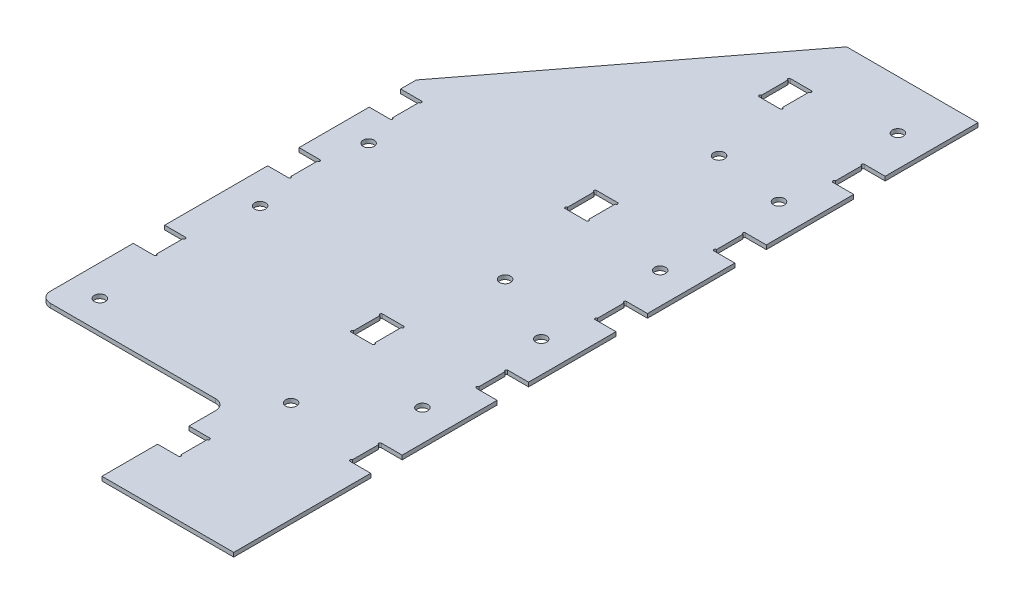
SolidWorks part; units mm, degrees
material "Ti-6Al-4VSolution treated and aged (SS)"
ref_plane "Front Plane" through (0, 0, 0) normal (0, 0, 1) x (1, 0, 0)
ref_plane "Top Plane" through (0, 0, 0) normal (0, 1, 0) x (1, 0, 0)
ref_plane "Right Plane" through (0, 0, 0) normal (1, 0, 0) x (0, 0, -1)
sketch "Sketch1" plane through (0, 0, 0) normal (0, 1, 0) x (1, 0, 0)
  line L0 (0, 0) -> (-80.9625, 0)
  line L1 (-80.9625, 0) -> (-80.9625, 76.2)
  line L3 (-80.9625, 76.2) -> (-195.2625, 76.2)
  line L5 (-195.2625, 76.2) -> (-195.2625, 307.3581)
  line L6 (-195.2625, 307.3581) -> (-80.645, 457.2)
  line L7 (-80.645, 457.2) -> (0, 457.2)
  line L8 (0, 457.2) -> (0, 0)
  dimension "D1" = 76.2
  dimension "D2" = 114.3
  dimension "D3" = 80.9625
  dimension "D4" = 457.2
  dimension "D5" = 231.1581
  dimension "D6" = 80.645
extrude "Boss-Extrude1" add sketch "Sketch1" along normal blind 2.54
fillet "Fillet1" radius 6.35 2 edges at (-195.2625, 1.27, -76.2) (-80.9625, 1.27, -76.2)
sketch "Sketch2" plane through (0, 2.54, 0) normal (0, 1, 0) x (1, 0, 0)
  line L0 (-80.9625, 69.85) -> (-80.9625, 0) construction
  line L1 (-68.2625, 34.29) -> (-80.9625, 34.29)
  line L2 (-68.2625, 34.29) -> (-68.2625, 53.34)
  line L3 (-68.2625, 53.34) -> (-80.9625, 53.34)
  line L4 (-80.9625, 34.29) -> (-80.9625, 53.34)
  line L5 (-80.9625, 53.34) -> (-68.2625, 53.34) construction
  line L6 (0, 0) -> (0, 457.2) construction
  line L7 (-12.7, 84.2962) -> (0, 84.2962)
  line L8 (-12.7, 84.2962) -> (-12.7, 103.3462)
  line L9 (-12.7, 103.3462) -> (0, 103.3462)
  line L10 (0, 84.2962) -> (0, 103.3462)
  line L11 (-12.7, 103.3462) -> (0, 103.3462) construction
  line L12 (-195.2625, 152.7175) -> (-182.5625, 152.7175) construction
  line L13 (-68.2625, 153.3525) -> (-80.9625, 153.3525)
  line L14 (-68.2625, 153.3525) -> (-68.2625, 172.4025)
  line L15 (-68.2625, 172.4025) -> (-80.9625, 172.4025)
  line L16 (-80.9625, 153.3525) -> (-80.9625, 172.4025)
  line L17 (-182.5625, 133.6675) -> (-195.2625, 133.6675)
  line L18 (-182.5625, 133.6675) -> (-182.5625, 152.7175)
  line L19 (-182.5625, 152.7175) -> (-195.2625, 152.7175)
  line L20 (-195.2625, 133.6675) -> (-195.2625, 152.7175)
  line L21 (-195.2625, 307.3581) -> (-195.2625, 82.55) construction
  line L22 (-195.2625, 235.2675) -> (-182.5625, 235.2675) construction
  line L23 (-182.5625, 216.2175) -> (-195.2625, 216.2175)
  line L24 (-182.5625, 216.2175) -> (-182.5625, 235.2675)
  line L25 (-182.5625, 235.2675) -> (-195.2625, 235.2675)
  line L26 (-195.2625, 216.2175) -> (-195.2625, 235.2675)
  line L27 (-195.2625, 297.6648) -> (-182.5625, 297.6648) construction
  line L28 (-182.5625, 278.6148) -> (-195.2625, 278.6148)
  line L29 (-182.5625, 278.6148) -> (-182.5625, 297.6648)
  line L30 (-182.5625, 297.6648) -> (-195.2625, 297.6648)
  line L31 (-195.2625, 278.6148) -> (-195.2625, 297.6648)
  line L32 (-12.7, 180.975) -> (0, 180.975) construction
  line L33 (-68.2625, 284.7975) -> (-80.9625, 284.7975)
  line L34 (-68.2625, 284.7975) -> (-68.2625, 303.8475)
  line L35 (-68.2625, 303.8475) -> (-80.9625, 303.8475)
  line L36 (-80.9625, 284.7975) -> (-80.9625, 303.8475)
  line L37 (-12.7, 161.925) -> (0, 161.925)
  line L38 (-12.7, 161.925) -> (-12.7, 180.975)
  line L39 (-12.7, 180.975) -> (0, 180.975)
  line L40 (0, 161.925) -> (0, 180.975)
  line L41 (-12.7, 254) -> (0, 254) construction
  line L42 (-12.7, 234.95) -> (0, 234.95)
  line L43 (-12.7, 234.95) -> (-12.7, 254)
  line L44 (-12.7, 254) -> (0, 254)
  line L45 (0, 234.95) -> (0, 254)
  line L46 (-12.7, 327.025) -> (0, 327.025) construction
  line L47 (-12.7, 307.975) -> (0, 307.975)
  line L48 (-12.7, 307.975) -> (-12.7, 327.025)
  line L49 (-12.7, 327.025) -> (0, 327.025)
  line L50 (0, 307.975) -> (0, 327.025)
  line L51 (-12.7, 400.05) -> (0, 400.05) construction
  line L52 (-12.7, 381) -> (0, 381)
  line L53 (-12.7, 381) -> (-12.7, 400.05)
  line L54 (-12.7, 400.05) -> (0, 400.05)
  line L55 (0, 381) -> (0, 400.05)
  line L56 (-81.0895, 403.733) -> (-81.0895, 423.037)
  line L57 (-80.9625, 403.86) -> (-68.2625, 403.86)
  line L58 (-80.9625, 403.86) -> (-80.9625, 422.91)
  line L59 (-80.9625, 422.91) -> (-68.2625, 422.91)
  line L60 (-68.2625, 403.86) -> (-68.2625, 422.91)
  line L61 (-81.0895, 423.037) -> (-68.1355, 423.037)
  line L62 (-68.1355, 403.733) -> (-68.1355, 423.037)
  line L63 (-81.0895, 403.733) -> (-68.1355, 403.733)
  line L64 (-182.4355, 297.7918) -> (-195.3895, 297.7918)
  line L65 (-195.3895, 278.4878) -> (-195.3895, 297.7918)
  line L66 (-182.4355, 278.4878) -> (-195.3895, 278.4878)
  line L67 (-182.4355, 278.4878) -> (-182.4355, 297.7918)
  line L68 (-68.1355, 303.9745) -> (-81.0895, 303.9745)
  line L69 (-81.0895, 284.6705) -> (-81.0895, 303.9745)
  line L70 (-68.1355, 284.6705) -> (-81.0895, 284.6705)
  line L71 (-68.1355, 284.6705) -> (-68.1355, 303.9745)
  line L72 (-182.4355, 235.3945) -> (-195.3895, 235.3945)
  line L73 (-195.3895, 216.0905) -> (-195.3895, 235.3945)
  line L74 (-182.4355, 216.0905) -> (-195.3895, 216.0905)
  line L75 (-182.4355, 216.0905) -> (-182.4355, 235.3945)
  line L76 (-182.4355, 152.8445) -> (-195.3895, 152.8445)
  line L77 (-195.3895, 133.5405) -> (-195.3895, 152.8445)
  line L78 (-182.4355, 133.5405) -> (-195.3895, 133.5405)
  line L79 (-182.4355, 133.5405) -> (-182.4355, 152.8445)
  line L80 (-68.1355, 172.5295) -> (-81.0895, 172.5295)
  line L81 (-81.0895, 153.2255) -> (-81.0895, 172.5295)
  line L82 (-68.1355, 153.2255) -> (-81.0895, 153.2255)
  line L83 (-68.1355, 153.2255) -> (-68.1355, 172.5295)
  line L84 (-68.1355, 53.467) -> (-81.0895, 53.467)
  line L85 (-81.0895, 34.163) -> (-81.0895, 53.467)
  line L86 (-68.1355, 34.163) -> (-81.0895, 34.163)
  line L87 (-68.1355, 34.163) -> (-68.1355, 53.467)
  line L88 (-12.827, 103.4732) -> (0.127, 103.4732)
  line L89 (0.127, 84.1692) -> (0.127, 103.4732)
  line L90 (-12.827, 84.1692) -> (0.127, 84.1692)
  line L91 (-12.827, 84.1692) -> (-12.827, 103.4732)
  line L92 (-12.827, 181.102) -> (0.127, 181.102)
  line L93 (0.127, 161.798) -> (0.127, 181.102)
  line L94 (-12.827, 161.798) -> (0.127, 161.798)
  line L95 (-12.827, 161.798) -> (-12.827, 181.102)
  line L96 (-12.827, 254.127) -> (0.127, 254.127)
  line L97 (0.127, 234.823) -> (0.127, 254.127)
  line L98 (-12.827, 234.823) -> (0.127, 234.823)
  line L99 (-12.827, 234.823) -> (-12.827, 254.127)
  line L100 (-12.827, 327.152) -> (0.127, 327.152)
  line L101 (0.127, 307.848) -> (0.127, 327.152)
  line L102 (-12.827, 307.848) -> (0.127, 307.848)
  line L103 (-12.827, 307.848) -> (-12.827, 327.152)
  line L104 (-12.827, 400.177) -> (0.127, 400.177)
  line L105 (0.127, 380.873) -> (0.127, 400.177)
  line L106 (-12.827, 380.873) -> (0.127, 380.873)
  line L107 (-12.827, 380.873) -> (-12.827, 400.177)
  dimension "D1" = 0.127
extrude "Cut-Extrude1" cut sketch "Sketch2" against normal through all
hole_wizard "1/4 Clearance Hole1" positions "Sketch4" profile "Sketch3" hole size "1/4" standard "ANSI Inch" end condition through all
sketch "Sketch4" plane through (0, 0, 0) normal (0, -1, 0) x (-1, 0, 0)
  point P0 (61.9125, 97.155)
  point P3 (19.05, 134.9375)
  point P6 (19.05, 207.9625)
  point P9 (61.9125, 228.6)
  point P12 (19.05, 280.9875)
  point P15 (19.05, 354.0125)
  point P18 (61.9125, 360.045)
  point P21 (19.05, 427.0375)
  point P24 (176.2125, 259.08)
  point P27 (176.2125, 192.405)
  point P30 (176.2125, 93.98)
sketch "Sketch3" plane through (-61.9125, 0, -97.155) normal (1, 0, 0) x (0, 0, -1)
  line L0 (0, 0) -> (0, 2.54)
  line L1 (0, 2.54) -> (3.3782, 2.54)
  line L2 (3.3782, 2.54) -> (3.3782, 0)
  line L5 (3.3782, 0) -> (0, 0)
  line L11 (0, -6.35) -> (0, 107.95) construction
  dimension "Thru Hole Dia." = 6.7564
  dimension "Thru Hole Depth" = 2.54
sketch "Sketch5" plane through (0, 2.54, 0) normal (0, 1, 0) x (1, 0, 0)
  line L0 (-182.4355, 278.4878) -> (-182.4355, 297.7918) construction
  line L1 (-182.4355, 216.0905) -> (-182.4355, 235.3945) construction
  line L2 (-182.4355, 133.5405) -> (-182.4355, 152.8445) construction
  line L3 (-68.1355, 34.163) -> (-68.1355, 53.467) construction
  line L4 (-12.827, 103.4732) -> (-12.827, 84.1692) construction
  line L5 (-68.1355, 153.2255) -> (-68.1355, 172.5295) construction
  line L6 (-81.0895, 172.5295) -> (-81.0895, 153.2255) construction
  line L7 (-12.827, 181.102) -> (-12.827, 161.798) construction
  line L8 (-12.827, 254.127) -> (-12.827, 234.823) construction
  line L9 (-68.1355, 284.6705) -> (-68.1355, 303.9745) construction
  line L10 (-81.0895, 303.9745) -> (-81.0895, 284.6705) construction
  line L11 (-12.827, 327.152) -> (-12.827, 307.848) construction
  line L12 (-12.827, 400.177) -> (-12.827, 380.873) construction
  line L13 (-68.1355, 403.733) -> (-68.1355, 423.037) construction
  line L14 (-81.0895, 423.037) -> (-81.0895, 403.733) construction
  circle A0 centre (-182.4355, 296.9981) radius 0.7938
  circle A1 centre (-182.4355, 279.2816) radius 0.7938
  circle A2 centre (-182.4355, 234.6007) radius 0.7938
  circle A3 centre (-182.4355, 216.8842) radius 0.7938
  circle A4 centre (-182.4355, 152.0507) radius 0.7938
  circle A5 centre (-182.4355, 134.3342) radius 0.7938
  circle A6 centre (-68.1355, 52.6732) radius 0.7937
  circle A7 centre (-68.1355, 34.9567) radius 0.7937
  circle A8 centre (-12.827, 84.963) radius 0.7937
  circle A9 centre (-12.827, 102.6795) radius 0.7937
  circle A10 centre (-68.1355, 171.7357) radius 0.7937
  circle A11 centre (-81.0895, 171.7357) radius 0.7937
  circle A12 centre (-81.0895, 154.0192) radius 0.7937
  circle A13 centre (-68.1355, 154.0192) radius 0.7937
  circle A14 centre (-12.827, 162.5917) radius 0.7937
  circle A15 centre (-12.827, 180.3082) radius 0.7937
  circle A16 centre (-12.827, 235.6167) radius 0.7937
  circle A17 centre (-12.827, 253.3332) radius 0.7938
  circle A18 centre (-68.1355, 285.4642) radius 0.7937
  circle A19 centre (-81.0895, 285.4642) radius 0.7937
  circle A20 centre (-81.0895, 303.1807) radius 0.7937
  circle A21 centre (-68.1355, 303.1807) radius 0.7937
  circle A22 centre (-12.827, 308.6418) radius 0.7938
  circle A23 centre (-12.827, 326.3582) radius 0.7938
  circle A24 centre (-12.827, 399.3833) radius 0.7938
  circle A25 centre (-12.827, 381.6667) radius 0.7938
  circle A26 centre (-68.1355, 422.2432) radius 0.7937
  circle A27 centre (-81.0895, 422.2432) radius 0.7937
  circle A28 centre (-81.0895, 404.5267) radius 0.7937
  circle A29 centre (-68.1355, 404.5267) radius 0.7937
  dimension "D1" = 1.5875
extrude "Cut-Extrude2" cut sketch "Sketch5" against normal through all
